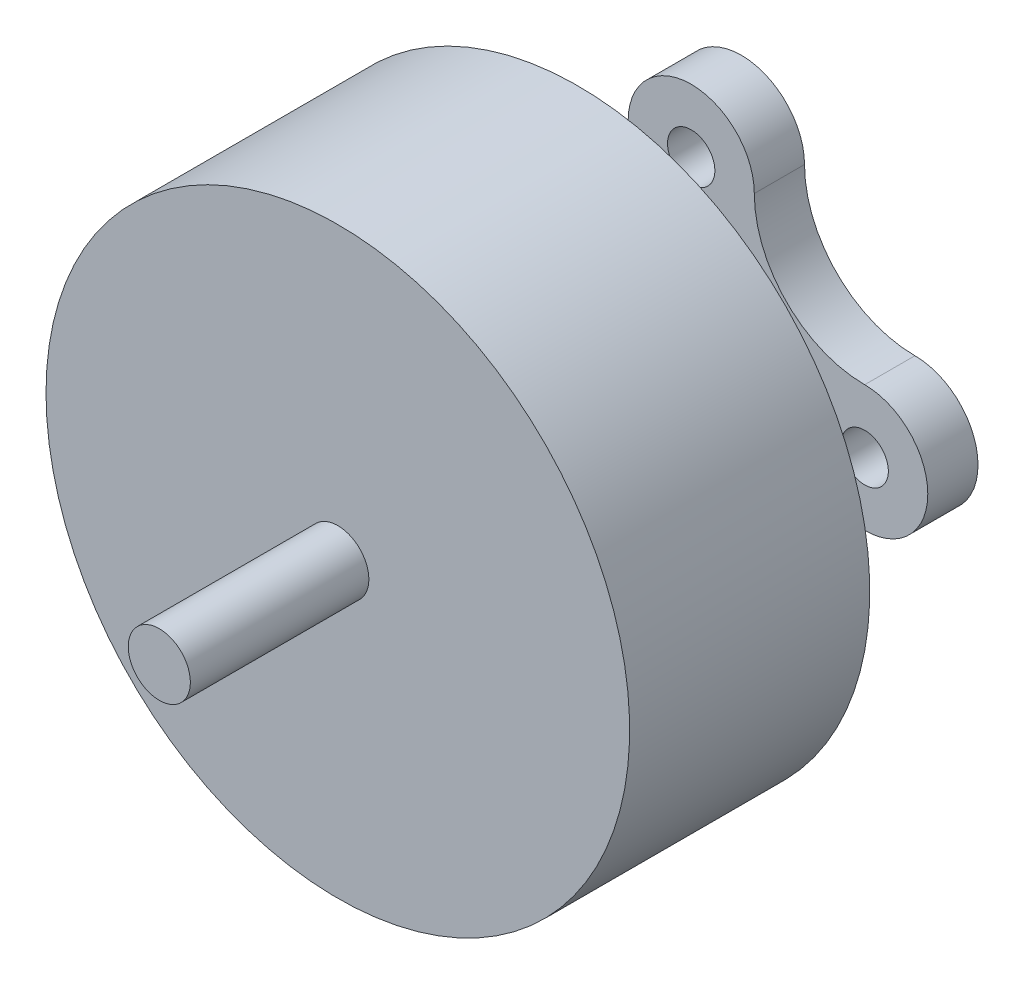
SolidWorks part; units mm, degrees
ref_plane "Front Plane" through (0, 0, 0) normal (0, 0, 1) x (1, 0, 0)
ref_plane "Top Plane" through (0, 0, 0) normal (0, 1, 0) x (1, 0, 0)
ref_plane "Right Plane" through (0, 0, 0) normal (1, 0, 0) x (0, 0, -1)
sketch "Sketch1" plane through (0, 0, 0) normal (0, 0, 1) x (1, 0, 0)
  circle A0 centre (0, 0) radius 9.4
  dimension "D1" = 18.8
extrude "Boss-Extrude1" add sketch "Sketch1" along normal blind 13
sketch "Sketch2" plane through (0, 0, 13) normal (0, 0, 1) x (1, 0, 0)
  circle A0 centre (0, 0) radius 1
  dimension "D1" = 2
extrude "Boss-Extrude2" add sketch "Sketch2" along normal blind 5.75
sketch "Sketch3" plane through (0, 0, 0) normal (0, 1, 0) x (1, 0, 0)
  line L0 (9.4, -13) -> (9.4, 0) construction
  line L1 (9.4, -1.6173) -> (1.6829, -1.6173)
  line L2 (9.4, -1.6173) -> (9.4, -5.2664)
  line L3 (9.4, -5.2664) -> (1.6829, -5.2664)
  line L4 (1.6829, -1.6173) -> (1.6829, -5.2664)
  line L5 (0, 0) -> (0, -18.75) construction
  line L6 (-1, -18.75) -> (1, -18.75) construction
revolve "Cut-Revolve1" cut sketch "Sketch3" angle 360 about L5
sketch "Sketch4" plane through (0, 0, 0) normal (0, 0, -1) x (-1, 0, 0)
  line L0 (0, 0) -> (0, 5.588) construction
  line L1 (0, 5.588) -> (0, 7.62)
  line L2 (0, 0) -> (5.588, 0) construction
  line L3 (5.588, 0) -> (7.62, 0)
  line L4 (0, -5.588) -> (0, -7.62)
  line L5 (-5.588, 0) -> (-7.62, 0)
  line L6 (0, 5.588) -> (0, 7.62)
  arc A0 (0, 7.62) -> (2.032, 5.588) centre (0, 5.588) cw
  arc A1 (5.588, 2.032) -> (7.62, 0) centre (5.588, 0) cw
  arc A2 (2.032, 5.588) -> (5.588, 2.032) centre (5.588, 5.588) ccw
  arc A3 (2.032, -5.588) -> (0, -7.62) centre (0, -5.588) cw
  arc A4 (5.588, -2.032) -> (2.032, -5.588) centre (5.588, -5.588) ccw
  arc A5 (7.62, 0) -> (5.588, -2.032) centre (5.588, 0) cw
  arc A6 (-5.588, -2.032) -> (-7.62, 0) centre (-5.588, 0) cw
  arc A7 (-2.032, -5.588) -> (-5.588, -2.032) centre (-5.588, -5.588) ccw
  arc A8 (0, -7.62) -> (-2.032, -5.588) centre (0, -5.588) cw
  arc A9 (-2.032, 5.588) -> (0, 7.62) centre (0, 5.588) cw
  arc A10 (-5.588, 2.032) -> (-2.032, 5.588) centre (-5.588, 5.588) ccw
  arc A11 (-7.62, 0) -> (-5.588, 2.032) centre (-5.588, 0) cw
  circle A12 centre (0, 5.588) radius 0.762
  circle A13 centre (5.588, 0) radius 0.762
  circle A14 centre (0, -5.588) radius 0.762
  circle A15 centre (-5.588, 0) radius 0.762
  point P33 (0, 0)
  point P41 (0, 0)
  dimension "D1" = 5.588
  dimension "D2" = 2.032
  dimension "D3" = 2.032
  dimension "D5" = 4
  dimension "D6" = 1.524
  dimension "D4" = 5.588
  dimension "D7" = 4
extrude "Cut-Extrude1" cut sketch "Sketch4" against normal up to surface (1.6173 mm away)
